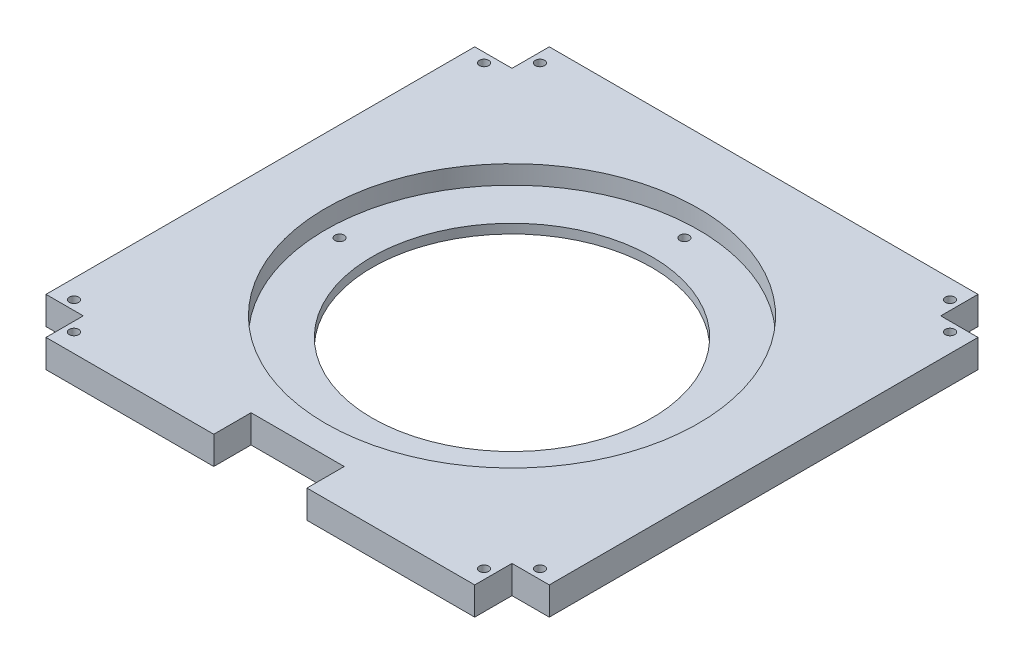
SolidWorks part; units mm, degrees
ref_plane "Front Plane" through (0, 0, 0) normal (0, 0, 1) x (1, 0, 0)
ref_plane "Top Plane" through (0, 0, 0) normal (0, 1, 0) x (1, 0, 0)
ref_plane "Right Plane" through (0, 0, 0) normal (1, 0, 0) x (0, 0, -1)
sketch "Sketch1" plane through (0, 0, 0) normal (0, 1, 0) x (1, 0, 0)
  line L21 (0, 0) -> (270, 0)
  line L22 (0, 0) -> (0, 270)
  line L23 (0, 270) -> (270, 270)
  line L24 (270, 0) -> (270, 270)
  line L44 (135, 270) -> (135, 0) construction
  line L45 (0, 135) -> (270, 135) construction
  dimension "D1" = 270
  dimension "D2" = 270
extrude "Boss-Extrude1" add sketch "Sketch1" along normal blind 15
sketch "Sketch8" plane through (0, 15, 0) normal (0, 1, 0) x (1, 0, 0)
  line L1 (0, 270) -> (20, 270)
  line L2 (0, 270) -> (0, 250)
  line L3 (0, 250) -> (20, 250)
  line L4 (20, 270) -> (20, 250)
  line L5 (270, 270) -> (250, 270)
  line L6 (270, 270) -> (270, 250)
  line L7 (270, 250) -> (250, 250)
  line L8 (250, 270) -> (250, 250)
  line L9 (270, 0) -> (250, 0)
  line L10 (270, 0) -> (270, 20)
  line L11 (270, 20) -> (250, 20)
  line L12 (250, 0) -> (250, 20)
  line L13 (0, 0) -> (20, 0)
  line L14 (0, 0) -> (0, 20)
  line L15 (0, 20) -> (20, 20)
  line L16 (20, 0) -> (20, 20)
  dimension "D1" = 20
  dimension "D2" = 20
  dimension "D3" = 20
  dimension "D4" = 20
  dimension "D5" = 20
  dimension "D6" = 20
  dimension "D7" = 20
  dimension "D8" = 20
extrude "Cut-Extrude1" cut sketch "Sketch8" against normal through all
sketch "Sketch9" plane through (0, 15, 0) normal (0, 1, 0) x (1, 0, 0)
  line L0 (135, 270) -> (135, 0) construction
  line L1 (250, 270) -> (20, 270) construction
  line L2 (20, 0) -> (250, 0) construction
  line L3 (0, 135) -> (270, 135) construction
  line L4 (0, 250) -> (0, 20) construction
  line L5 (270, 20) -> (270, 250) construction
  line L6 (260, 250) -> (260, 20) construction
  line L7 (250, 250) -> (270, 250) construction
  line L8 (270, 20) -> (250, 20) construction
  line L9 (250, 10) -> (20, 10) construction
  line L10 (250, 20) -> (250, 0) construction
  line L11 (20, 0) -> (20, 20) construction
  line L12 (10, 250) -> (10, 20) construction
  line L13 (0, 250) -> (20, 250) construction
  line L14 (20, 20) -> (0, 20) construction
  line L15 (20, 260) -> (250, 260) construction
  line L16 (20, 250) -> (20, 270) construction
  line L17 (250, 270) -> (250, 250) construction
  circle A0 centre (10, 245) radius 2.5
  circle A1 centre (10, 25) radius 2.5
  circle A2 centre (25, 10) radius 2.5
  circle A3 centre (245, 10) radius 2.5
  circle A4 centre (260, 25) radius 2.5
  circle A5 centre (260, 245) radius 2.5
  circle A6 centre (245, 260) radius 2.5
  circle A7 centre (25, 260) radius 2.5
  dimension "D1" = 5
  dimension "D2" = 5
  dimension "D3" = 5
  dimension "D4" = 5
  dimension "D5" = 5
  dimension "D6" = 5
  dimension "D7" = 5
  dimension "D8" = 5
  dimension "D9" = 5
  dimension "D10" = 5
  dimension "D11" = 5
  dimension "D12" = 5
  dimension "D13" = 5
  dimension "D14" = 5
  dimension "D15" = 5
  dimension "D16" = 5
extrude "Cut-Extrude2" cut sketch "Sketch9" against normal through all
sketch "Sketch10" plane through (0, 15, 0) normal (0, 1, 0) x (1, 0, 0)
  line L0 (135, 270) -> (135, 0) construction
  line L2 (250, 270) -> (20, 270) construction
  line L3 (20, 0) -> (250, 0) construction
  line L4 (0, 135) -> (270, 135) construction
  line L5 (0, 250) -> (0, 20) construction
  line L6 (270, 20) -> (270, 250) construction
  circle A0 centre (135, 135) radius 100
  dimension "D1" = 200
extrude "Cut-Extrude3" cut sketch "Sketch10" against normal blind 10
sketch "Sketch12" plane through (0, 5, 0) normal (0, 1, 0) x (1, 0, 0)
  line L0 (135, 235) -> (135, 35) construction
  line L1 (35, 135) -> (235, 135) construction
  circle A0 centre (135, 135) radius 100 construction
  circle A1 centre (135, 135) radius 100 construction
  circle A2 centre (135, 135) radius 75
  circle A3 centre (135, 227.5) radius 2.5
  circle A4 centre (227.5, 135) radius 2.5
  circle A5 centre (135, 42.5) radius 2.5
  circle A6 centre (42.5, 135) radius 2.5
  dimension "D1" = 150
  dimension "D2" = 5
  dimension "D3" = 5
  dimension "D4" = 5
  dimension "D5" = 5
  dimension "D6" = 92.5
  dimension "D7" = 92.5
  dimension "D8" = 92.5
  dimension "D9" = 92.5
extrude "Cut-Extrude4" cut sketch "Sketch12" against normal through all
sketch "Sketch13" plane through (0, 15, 0) normal (0, 1, 0) x (1, 0, 0)
  line L0 (135, 270) -> (135, 0) construction
  line L1 (250, 270) -> (20, 270) construction
  line L2 (20, 0) -> (250, 0) construction
  line L3 (0, 135) -> (270, 135) construction
  line L4 (0, 250) -> (0, 20) construction
  line L5 (270, 20) -> (270, 250) construction
  line L7 (110, 0) -> (160, 0)
  line L8 (110, 0) -> (110, 20)
  line L9 (110, 20) -> (160, 20)
  line L10 (160, 0) -> (160, 20)
  dimension "D1" = 20
  dimension "D2" = 50
  dimension "D3" = 25
  dimension "D4" = 25
extrude "Cut-Extrude5" cut sketch "Sketch13" against normal up to surface (15 mm away) up to face at (135, 0, -225)
